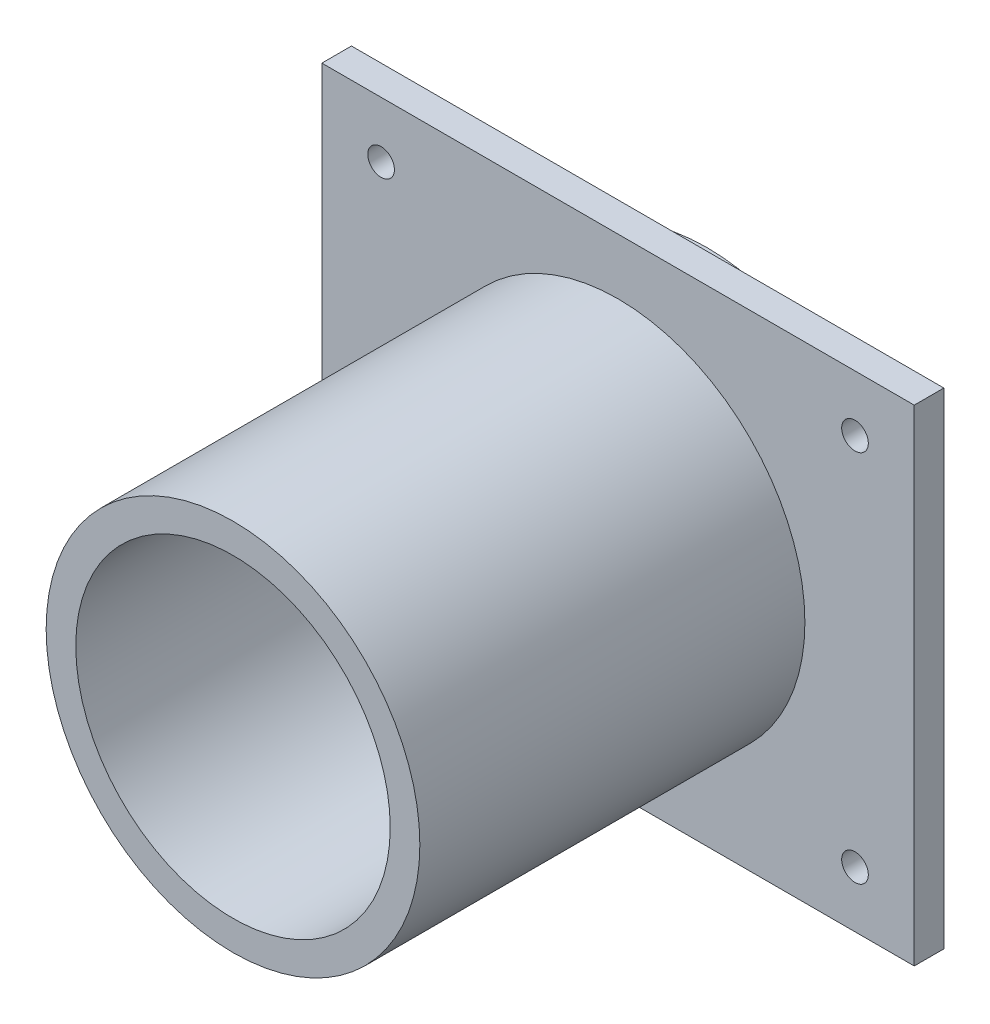
SolidWorks part; units mm, degrees
material "1060 Alloy"
ref_plane "Front Plane" through (0, 0, 0) normal (0, 0, 1) x (1, 0, 0)
ref_plane "Top Plane" through (0, 0, 0) normal (0, 1, 0) x (1, 0, 0)
ref_plane "Right Plane" through (0, 0, 0) normal (1, 0, 0) x (0, 0, -1)
sketch "Sketch1" plane through (0, 0, 0) normal (0, 0, 1) x (1, 0, 0)
  circle A0 centre (0, 0) radius 26.543
  circle A1 centre (0, 0) radius 31.543
  dimension "D1" = 53.086
  dimension "D2" = 5
extrude "Boss-Extrude1" add sketch "Sketch1" against normal blind 10
sketch "Sketch2" plane through (0, 0, 0) normal (0, 0, 1) x (1, 0, 0)
  line L1 (-50, -41) -> (50, -41)
  line L2 (-50, -41) -> (-50, 41)
  line L3 (-50, 41) -> (50, 41)
  line L4 (50, -41) -> (50, 41)
  line L5 (-50, -41) -> (50, 41) construction
  line L6 (-50, 41) -> (50, -41) construction
  point P0 (0, 0)
  dimension "D1" = 82
  dimension "D2" = 100
extrude "Boss-Extrude2" add sketch "Sketch2" along normal blind 5
hole_wizard "M4 Clearance Hole2" positions "Sketch6" profile "Sketch7" hole size "M4" standard "ANSI Metric" end condition up to next
sketch "Sketch6" plane through (0, 0, 0) normal (0, 0, -1) x (-1, 0, 0)
  line L0 (-40, 31.543) -> (40, 31.543)
  line L2 (-40, -31.543) -> (40, -31.543)
  line L5 (0, 8.25) -> (0, -8.25) construction
  circle A0 centre (0, 0) radius 31.543 construction
  circle A1 centre (0, 0) radius 31.543 construction
  point P0 (-40, 31.543)
  point P2 (40, 31.543)
  point P4 (40, -31.543)
  point P6 (-40, -31.543)
  dimension "D1" = 40
  dimension "D2" = 40
sketch "Sketch7" plane through (40, 31.543, 0) normal (1, 0, 0) x (0, 1, 0)
  line L0 (0, 0) -> (0, 5)
  line L1 (0, 5) -> (2.25, 5)
  line L2 (2.25, 5) -> (2.25, 0)
  line L5 (2.25, 0) -> (0, 0)
  line L11 (0, -6.35) -> (0, 107.95) construction
  dimension "Thru Hole Dia." = 4.5
  dimension "Thru Hole Depth" = 5
sketch "Sketch8" plane through (0, 0, 5) normal (0, 0, 1) x (1, 0, 0)
  circle A0 centre (0, 0) radius 31.543
  circle A1 centre (0, 0) radius 26.543
  dimension "D1" = 53.086
  dimension "D2" = 5
extrude "Boss-Extrude3" add sketch "Sketch8" along normal blind 65
